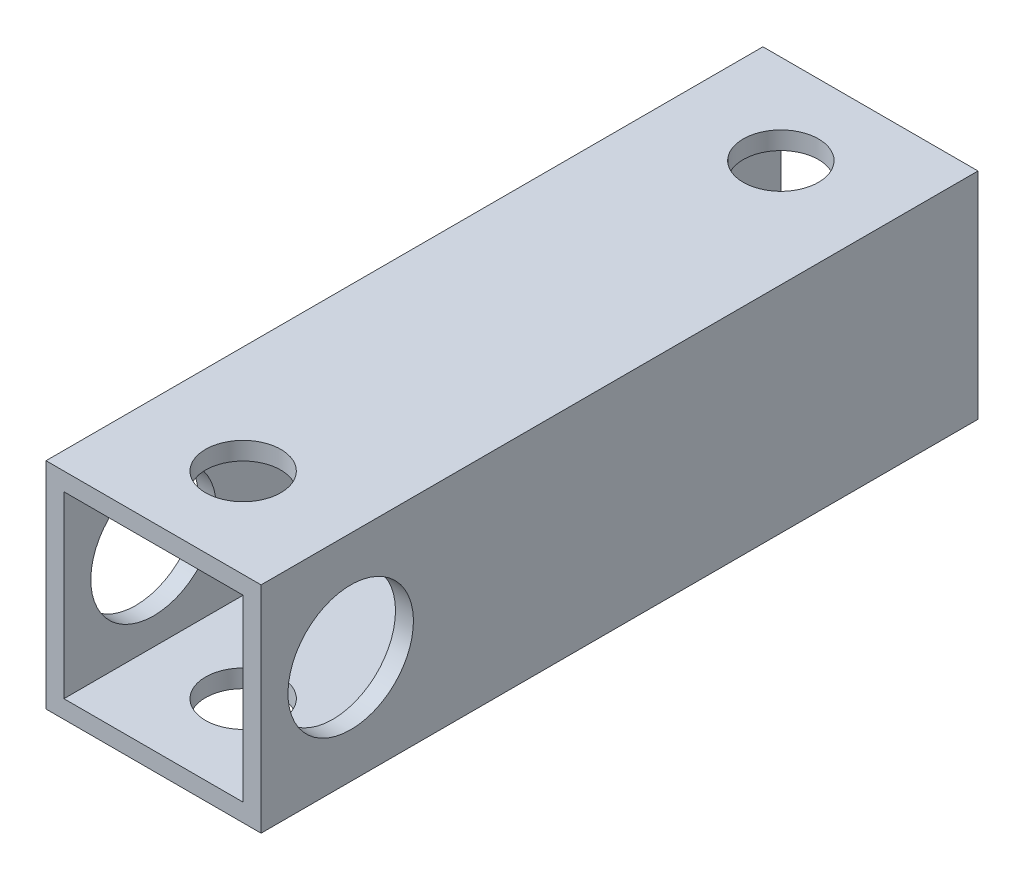
SolidWorks part; units mm, degrees
ref_plane "正面" through (0, 0, 0) normal (0, 0, 1) x (1, 0, 0)
ref_plane "平面" through (0, 0, 0) normal (0, 1, 0) x (1, 0, 0)
ref_plane "右側面" through (0, 0, 0) normal (1, 0, 0) x (0, 0, -1)
sketch "ｽｹｯﾁ1" plane through (0, 0, 0) normal (0, 0, 1) x (1, 0, 0)
  line L1 (-6, 6) -> (6, 6)
  line L2 (-6, 6) -> (-6, -6)
  line L3 (-6, -6) -> (6, -6)
  line L4 (6, 6) -> (6, -6)
  line L5 (-6, 6) -> (6, -6) construction
  line L6 (-6, -6) -> (6, 6) construction
  point P0 (0, 0)
  dimension "D1" = 12
  dimension "D2" = 12
extrude "ﾎﾞｽ - 押し出し1" add sketch "ｽｹｯﾁ1" along normal blind 40
sketch "ｽｹｯﾁ2" plane through (0, 0, 40) normal (0, 0, 1) x (1, 0, 0)
  line L1 (-5, 5) -> (5, 5)
  line L2 (-5, 5) -> (-5, -5)
  line L3 (-5, -5) -> (5, -5)
  line L4 (5, 5) -> (5, -5)
  line L5 (-5, 5) -> (5, -5) construction
  line L6 (-5, -5) -> (5, 5) construction
  point P0 (0, 0)
  dimension "D1" = 10
  dimension "D2" = 10
extrude "ｶｯﾄ - 押し出し1" cut sketch "ｽｹｯﾁ2" against normal blind 47.5
sketch "ｽｹｯﾁ3" plane through (0, 6, 0) normal (0, 1, 0) x (1, 0, 0)
  line L0 (0, 0) -> (0, -5)
  line L1 (0, -40) -> (0, -35)
  line L2 (6, -40) -> (-6, -40) construction
  circle A0 centre (0, -5) radius 2.1
  circle A1 centre (0, -35) radius 2.1
  dimension "D2" = 4.2
  dimension "D4" = 4.2
  dimension "D1" = 5
  dimension "D3" = 5
extrude "ｶｯﾄ - 押し出し2" cut sketch "ｽｹｯﾁ3" against normal blind 47.5
sketch "ｽｹｯﾁ4" plane through (-6, 0, 0) normal (-1, 0, 0) x (0, 0, 1)
  line L0 (0, 0) -> (5, 0)
  circle A0 centre (5, 0) radius 4
  dimension "D2" = 8
  dimension "D1" = 5
sketch "ｽｹｯﾁ5" plane through (-6, 0, 0) normal (-1, 0, 0) x (0, 0, 1)
  line L0 (40, 0) -> (35, 0)
  line L1 (40, 6) -> (40, -6) construction
  circle A0 centre (35, 0) radius 3.5
  dimension "D2" = 7
  dimension "D1" = 5
extrude "ｶｯﾄ - 押し出し4" cut sketch "ｽｹｯﾁ5" against normal blind 47.5
